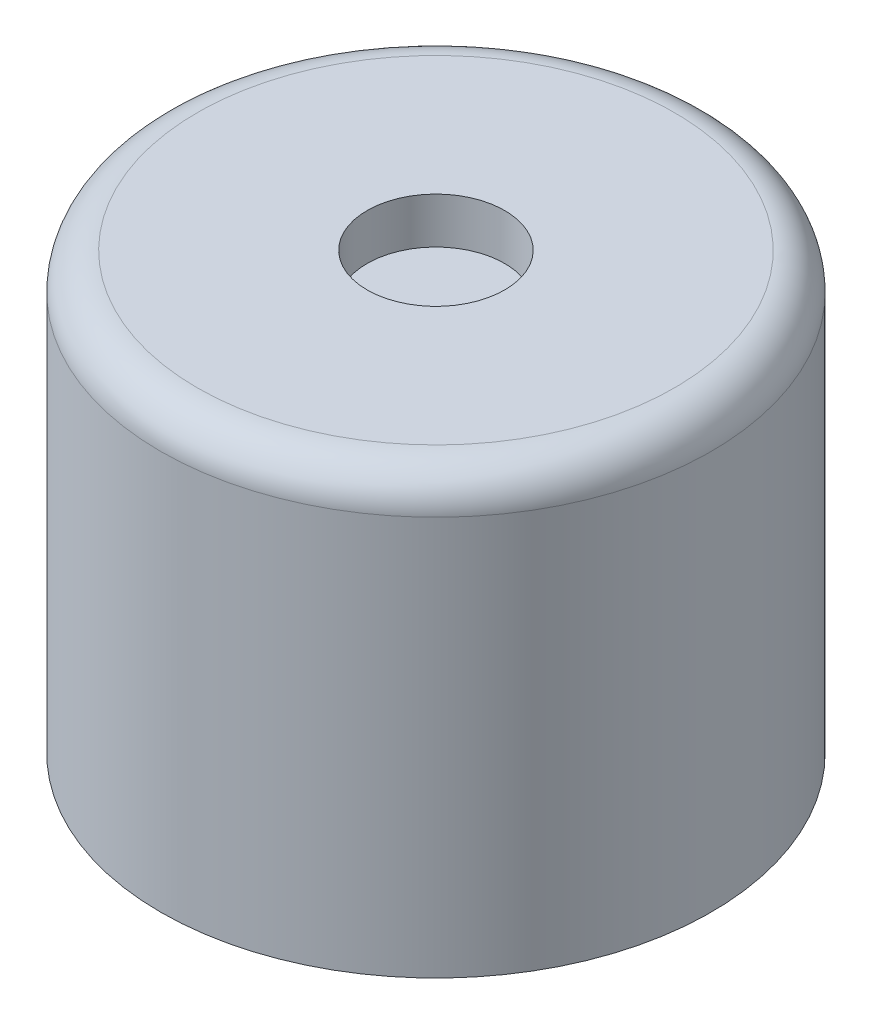
SolidWorks part; units mm, degrees
ref_plane "Front Plane" through (0, 0, 0) normal (0, 0, 1) x (1, 0, 0)
ref_plane "Top Plane" through (0, 0, 0) normal (0, 1, 0) x (1, 0, 0)
ref_plane "Right Plane" through (0, 0, 0) normal (1, 0, 0) x (0, 0, -1)
sketch "Sketch1" plane through (0, 0, 0) normal (0, 1, 0) x (1, 0, 0)
  circle A0 centre (0, 0) radius 6
  dimension "D1" = 12
extrude "Boss-Extrude1" add sketch "Sketch1" along normal blind 9.5
ref_plane "Plane1" through (0, 9.5, 0) normal (0, 1, 0) x (1, 0, 0)
sketch "Sketch2" plane through (0, 9.5, 0) normal (0, 1, 0) x (1, 0, 0)
  circle A0 centre (0, 0) radius 1.5
extrude "Cut-Extrude1" cut sketch "Sketch2" against normal blind 1
fillet "Fillet1" radius 0.8 1 edges at (0, 9.5, 6)
